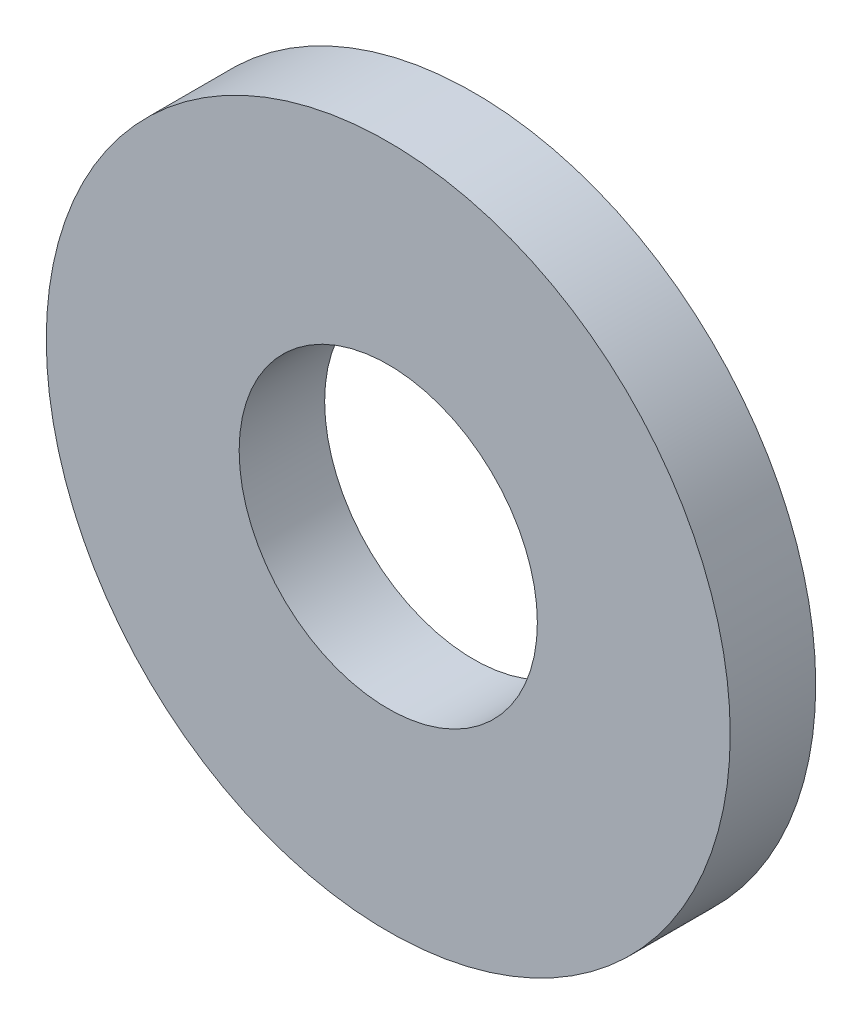
SolidWorks part; units mm, degrees
material "SS 304 (Default)"
ref_plane "Front Plane" through (0, 0, 0) normal (0, 0, 1) x (1, 0, 0)
ref_plane "Top Plane" through (0, 0, 0) normal (0, 1, 0) x (1, 0, 0)
ref_plane "Right Plane" through (0, 0, 0) normal (1, 0, 0) x (0, 0, -1)
sketch "Sketch1" plane through (0, 0, 0) normal (0, 0, 1) x (1, 0, 0)
  circle A0 centre (0, 0) radius 6.35
  circle A1 centre (0, 0) radius 2.7686
  dimension "D1" = 5.5372
  dimension "Diameter" = 12.7
extrude "Extrude1" add sketch "Sketch1" along normal mid plane 1.5875
